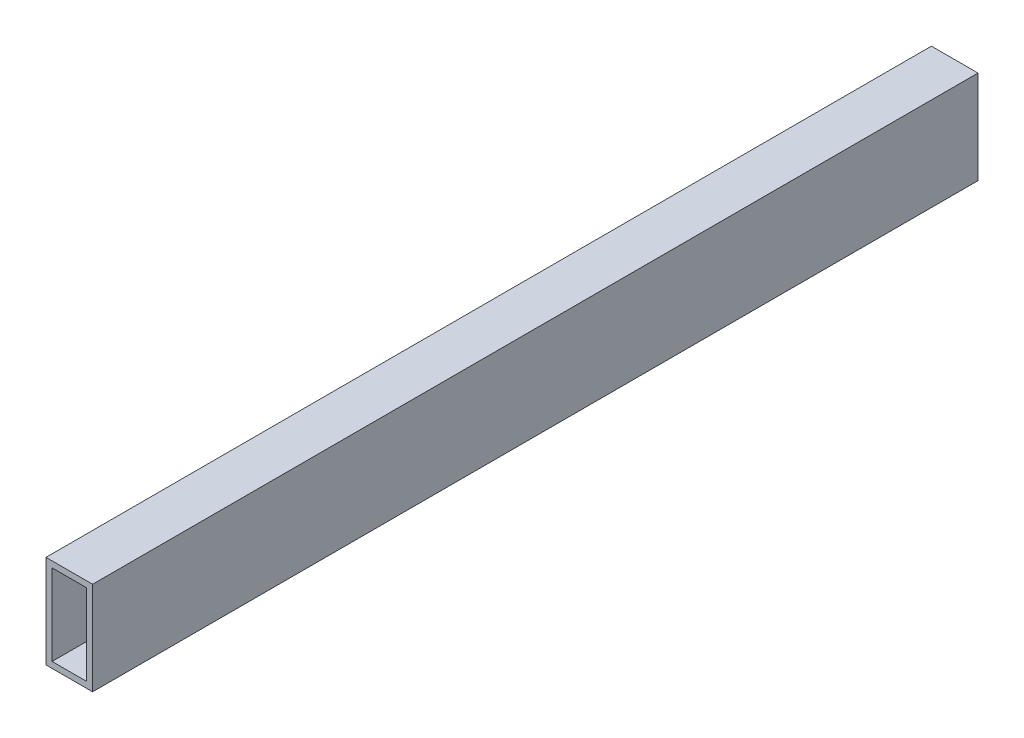
SolidWorks part; units mm, degrees
ref_plane "Front Plane" through (0, 0, 0) normal (0, 0, 1) x (1, 0, 0)
ref_plane "Top Plane" through (0, 0, 0) normal (0, 1, 0) x (1, 0, 0)
ref_plane "Right Plane" through (0, 0, 0) normal (1, 0, 0) x (0, 0, -1)
sketch "Sketch1" plane through (0, 0, 0) normal (0, 0, 1) x (1, 0, 0)
  line L1 (-12.7, 25.4) -> (12.7, 25.4)
  line L2 (-12.7, 25.4) -> (-12.7, -25.4)
  line L3 (-12.7, -25.4) -> (12.7, -25.4)
  line L4 (12.7, 25.4) -> (12.7, -25.4)
  line L5 (-12.7, 25.4) -> (12.7, -25.4) construction
  line L6 (-12.7, -25.4) -> (12.7, 25.4) construction
  line L7 (-9.398, 22.098) -> (9.398, 22.098)
  line L8 (-9.398, 22.098) -> (-9.398, -22.098)
  line L9 (-9.398, -22.098) -> (9.398, -22.098)
  line L10 (9.398, 22.098) -> (9.398, -22.098)
  line L11 (-9.398, 22.098) -> (9.398, -22.098) construction
  line L12 (-9.398, -22.098) -> (9.398, 22.098) construction
  point P0 (0, 0)
  point P6 (0, 0)
  dimension "D1" = 25.4
  dimension "D2" = 50.8
  dimension "D3" = 18.796
  dimension "D4" = 44.196
extrude "Boss-Extrude1" add sketch "Sketch1" along normal blind 482.6
